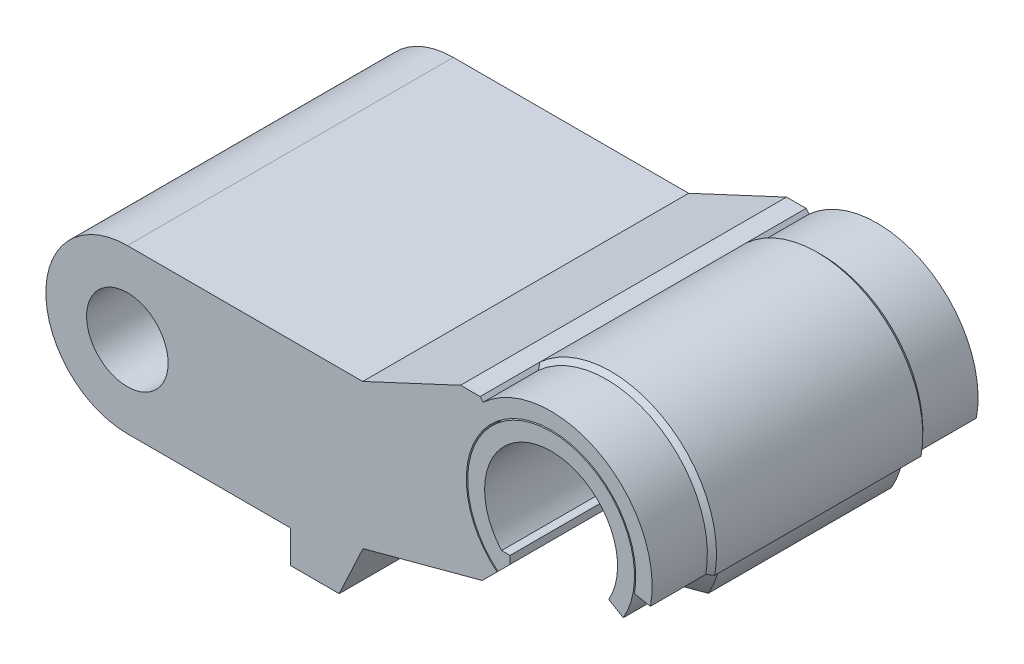
SolidWorks part; units mm, degrees
ref_plane "Front Plane" through (0, 0, 0) normal (0, 0, 1) x (1, 0, 0)
ref_plane "Top Plane" through (0, 0, 0) normal (0, 1, 0) x (1, 0, 0)
ref_plane "Right Plane" through (0, 0, 0) normal (1, 0, 0) x (0, 0, -1)
sketch "Sketch9" plane through (0, 0, 0) normal (0, 0, 1) x (1, 0, 0)
  line L0 (0, 0) -> (-40, 0) construction
  line L1 (-40, 0) -> (-40, -20) construction
  dimension "D1" = 20
  dimension "D2" = 40
sketch "Sketch1" plane through (0, 0, 0) normal (0, 0, 1) x (1, 0, 0)
  line L0 (7.5, -6.6144) -> (-7.5, -6.6144) construction
  line L1 (-7.5, -6.6144) -> (-6.3, -6.6144)
  line L2 (-6.3, -6.6144) -> (-6.3, 1.2617)
  line L3 (-6.3, 1.2617) -> (0, 4.899) construction
  line L4 (5, 4.899) -> (-5, 4.899) construction
  line L5 (0, -14.4444) -> (0, 14.4444) construction
  line L6 (-5.5, 5.199) -> (5.5, 5.199)
  line L7 (-6.3, 1.2617) -> (-3.7026, 2.7613)
  line L8 (0, 0) -> (-7.1429, 6.9985) construction
  line L9 (-5.5, 4.399) -> (-3.7026, 3.3613)
  line L10 (-5.5, 5.199) -> (-5.5, 4.399)
  line L11 (-3.7026, 3.3613) -> (-3.7026, 2.7613)
  line L12 (7.5, -6.6144) -> (6.3, -6.6144)
  line L13 (3.7026, 3.3613) -> (3.7026, 2.7613)
  line L14 (5.5, 5.199) -> (5.5, 4.399)
  line L15 (5.5, 4.399) -> (3.7026, 3.3613)
  line L16 (6.3, 1.2617) -> (3.7026, 2.7613)
  line L17 (6.3, -6.6144) -> (6.3, 1.2617)
  circle A0 centre (0, 0) radius 10 construction
  arc A1 (-7.5, -6.6144) -> (7.5, -6.6144) centre (0, 0) cw
  point P11 (0, 4.899)
  point P14 (0, 0)
sketch "Sketch2" plane through (0, 0, 0) normal (-1, 0, 0) x (0, 0, 1)
  line L0 (0, 10) -> (0, 15)
  line L3 (0, 15) -> (-3, 15)
  line L4 (-3, 15) -> (-9, 9)
  line L5 (-9, 9) -> (0, 9)
  line L6 (0, 9) -> (0, 10)
sketch "Sketch11" plane through (-40, -20, 0) normal (0, 0, -1) x (-1, 0, 0)
  line L0 (0, 0) -> (0, -150.5823)
  line L1 (0, 0) -> (15, 0)
  line L2 (15, 0) -> (43.25, -60.5823)
  line L3 (43.25, -60.5823) -> (53.25, -60.5823)
  line L4 (53.25, -60.5823) -> (53.25, -150.5823)
  line L5 (53.25, -150.5823) -> (72.25, -150.5823)
  line L6 (91.25, -150.5823) -> (91.25, -10.5823)
  line L7 (91.25, -10.5823) -> (114.25, -10.5823)
  line L8 (114.25, -10.5823) -> (114.25, -150.5823)
  line L9 (72.25, -150.5823) -> (91.25, -150.5823)
sketch "Sketch3" plane through (0, 0, 0) normal (0, 0, 1) x (1, 0, 0)
  line L0 (0, 15) -> (0, 15.2) construction
  line L1 (6.3, -8.0144) -> (9.8566, -11.571)
  line L2 (6.3, -6.8144) -> (6.3, -8.0144)
  line L16 (-6.3, -6.8144) -> (-6.3, -8.0144)
  line L17 (-6.3, -8.0144) -> (-9.8566, -11.571)
  line L18 (6.3, -6.8144) -> (7.5897, -6.8144)
  line L19 (-7.5897, -6.8144) -> (-6.3, -6.8144)
  line L20 (6.3, -6.8144) -> (7.5897, -6.8144)
  line L21 (-7.5897, -6.8144) -> (-6.3, -6.8144)
  arc A4 (-9.8566, -11.571) -> (9.8566, -11.571) centre (0, 0) cw
  arc A5 (7.5897, -6.8144) -> (-7.5897, -6.8144) centre (0, 0) ccw
  arc A6 (7.5897, -6.8144) -> (-7.5897, -6.8144) centre (0, 0) ccw
  point P4 (0, 15.1)
  point P5 (-10.1479, -11.3164)
  point P6 (-10.1104, -11.3499)
  point P10 (-9.8161, -11.5305)
  point P11 (0, 0)
  point P12 (0, 15.4202)
  dimension "D3" = 45
  dimension "D2" = 0.2
  dimension "D4" = 1.2
  dimension "D1" = 0.2
extrude "Boss-Extrude1" add sketch "Sketch3" along normal mid plane 50
sketch "Sketch4" plane through (0, 0, 0) normal (1, 0, 0) x (0, 0, -1)
  line L0 (0, 15) -> (0, 15.2) construction
  line L4 (-3.0828, 15.2) -> (-9.4828, 8.8)
  line L7 (9.4828, 8.8) -> (0, 8.8)
  line L8 (3.0828, 15.2) -> (9.4828, 8.8)
  line L9 (0, 15.2) -> (3.0828, 15.2)
  line L10 (9.4828, 8.8) -> (-9.4828, 8.8)
  line L11 (3.0828, 15.2) -> (9.4828, 8.8)
  line L12 (-3.0828, 15.2) -> (3.0828, 15.2)
  point P4 (0, 15.1878)
  dimension "D1" = 0.2
extrude "Cut-Extrude1" cut sketch "Sketch4" against normal mid plane 5.2
sketch "Sketch5" plane through (0, 0, 0) normal (1, 0, 0) x (0, 0, -1)
  line L0 (-25, 15.2) -> (-3.0828, 15.2)
  line L4 (3.0828, 15.2) -> (25, 15.2)
  line L5 (3.0828, 15.2) -> (25, 15.2) construction
  line L6 (25, 15.2) -> (25, 12.8)
  line L7 (25, 12.8) -> (16.4414, 12.8)
  line L8 (16.4414, 12.8) -> (14.0414, 15.2)
  line L9 (14.0414, 15.2) -> (25, 15.2)
  line L10 (25, 15.2) -> (3.0828, 15.2) construction
  line L11 (-27.2236, 0) -> (27.2236, 0) construction
  point P18 (0, 0)
  dimension "D1" = 45
  dimension "D2" = 2.4
revolve "Cut-Revolve1" cut sketch "Sketch5" angle 360 about L11
mirror "Mirror1" about plane through (0, 0, 0) normal (0, 0, 1) of "Cut-Revolve1"
sketch "Sketch7" plane through (0, 0, 0) normal (1, 0, 0) x (0, 0, -1)
  line L0 (16.4414, 12.8) -> (14.0414, 15.2)
  line L1 (16.4414, 12.8) -> (14.0414, 15.2) construction
  line L2 (25, 12.8) -> (16.4414, 12.8)
  line L3 (25, 12.8) -> (16.4414, 12.8) construction
  line L9 (-29.9525, 0) -> (29.9525, 0) construction
  line L10 (0, 0) -> (0, 27.8077) construction
  line L11 (-14.0414, 15.2) -> (-3.0828, 15.2)
  line L12 (3.0828, 15.2) -> (14.0414, 15.2)
  line L13 (3.0828, 15.2) -> (14.0414, 15.2) construction
  line L14 (25, 13) -> (16.5243, 13)
  line L15 (16.5243, 13) -> (14.1243, 15.4)
  line L16 (3.0828, 15.4) -> (14.1243, 15.4)
  line L17 (3.0828, 15.4) -> (-3.0828, 15.4)
  line L18 (-3.0828, 15.4) -> (-14.1243, 15.4)
  line L19 (-16.5243, 13) -> (-14.1243, 15.4)
  line L20 (-25, 13) -> (-16.5243, 13)
  line L22 (25, 13) -> (25, 15.5)
  line L23 (25, 15.5) -> (16.5243, 15.5)
  line L24 (16.5243, 15.5) -> (15.8243, 16.2)
  line L25 (15.8243, 16.2) -> (-15.8243, 16.2)
  line L26 (-3.0828, 15.2) -> (-14.0414, 15.2) construction
  line L27 (-16.4414, 12.8) -> (-14.0414, 15.2) construction
  line L28 (-16.5243, 15.5) -> (-15.8243, 16.2)
  line L29 (-25, 15.5) -> (-16.5243, 15.5)
  line L30 (-25, 13) -> (-25, 15.5)
  point P3 (16.8282, 16.2359)
  point P12 (0, 0)
  point P22 (0, 15.4)
  point P26 (0, 25)
  point P29 (15.3099, 16.2)
  point P32 (0, 16.2)
  dimension "D2" = 0.8
  dimension "D3" = 2.5
  dimension "D1" = 0.2
revolve "Revolve1" add sketch "Sketch7" angle 360 about L9
sketch "Sketch10" plane through (0, 0, 0) normal (0, 0, 1) x (1, 0, 0)
  line L0 (-6.3, -8.0144) -> (-9.8566, -11.571)
  line L1 (-6.3, -8.0144) -> (-9.8566, -11.571)
  line L2 (-9.8566, -11.571) -> (-28.2856, -30)
  line L5 (0, -14.4444) -> (0, 14.4444) construction
  line L6 (0, 0) -> (0, -30) construction
  line L9 (-6.3, -8.0144) -> (0, 0)
  line L10 (-28.2856, -30) -> (0, -30)
  line L11 (0, 0) -> (29.5047, -5.4288)
  line L12 (-9.8566, -11.571) -> (0, 0) construction
  arc A0 (29.5047, -5.4288) -> (0, -30) centre (0, 0) cw
  point P6 (0, -0.5784)
  dimension "D1" = 120
  dimension "D2" = 30
extrude "Cut-Extrude2" cut sketch "Sketch10" against normal through all both and the other way through all
sketch "Sketch12" plane through (0, 0, 0) normal (0, 0, 1) x (1, 0, 0)
  line L0 (-40, -20) -> (-40, -25)
  line L1 (-40, -20) -> (-40, -170.5823) construction
  line L2 (-40, -25) -> (-32.5, -25)
  line L3 (-32.5, -25) -> (-28.8537, -17.1804)
  line L4 (-28.8537, -17.1804) -> (-10.5658, -12.2802)
  line L5 (-9.9985, -11.7128) -> (-10.5658, -12.2802)
  line L6 (-9.9985, -11.7128) -> (-10.5658, -12.2802) construction
  line L7 (-40, -20) -> (-65, -20)
  line L8 (-28.8946, 5) -> (-65, 5)
  line L9 (-65, 5) -> (-65, -20) construction
  line L10 (-10.883, 12) -> (-13.883, 12)
  line L11 (-13.883, 12) -> (-28.8946, 5)
  arc A0 (15.9325, -2.9315) -> (-10.5658, -12.2802) centre (0, 0) ccw
  arc A1 (15.9325, -2.9315) -> (-10.5658, -12.2802) centre (0, 0) ccw construction
  arc A2 (-65, 5) -> (-65, -20) centre (-65, -7.5) ccw
  arc A3 (-10.883, 12) -> (-10.5658, -12.2802) centre (0, 0) ccw
  point P10 (0, 0)
  dimension "D1" = 5
  dimension "D2" = 7.5
  dimension "D3" = 115
  dimension "D4" = 130
  dimension "D5" = 10
  dimension "D6" = 25
  dimension "D7" = 3
  dimension "D8" = 25
  dimension "D9" = 7
extrude "Boss-Extrude2" add sketch "Sketch12" along normal mid plane 50
sketch "Sketch13" plane through (0, 0, -25) normal (0, 0, -1) x (-1, 0, 0)
  line L0 (10.883, 12) -> (10.4128, 11.4815)
  line L1 (10.0694, -11.7838) -> (10.5658, -12.2802)
  line L2 (-15.2441, -2.8049) -> (-12.7854, -2.3525)
  line L3 (8.2951, -10.0095) -> (10.0694, -11.7838)
  line L8 (40, -20) -> (65, -20)
  line L9 (65, 5) -> (28.8946, 5)
  line L10 (28.8946, 5) -> (13.883, 12)
  line L11 (13.883, 12) -> (10.883, 12)
  line L12 (10.5658, -12.2802) -> (28.8537, -17.1804)
  line L13 (28.8537, -17.1804) -> (32.5, -25)
  line L14 (32.5, -25) -> (40, -25)
  line L15 (40, -25) -> (40, -20)
  arc A0 (10.0694, -11.7838) -> (10.4128, 11.4815) centre (0, 0) ccw
  arc A2 (65, -20) -> (65, 5) centre (65, -7.5) ccw
  arc A3 (10.5658, -12.2802) -> (10.883, 12) centre (0, 0) ccw
  arc A5 (10.5658, -12.2802) -> (10.883, 12) centre (0, 0) ccw
  arc A6 (10.0694, -11.7838) -> (-15.2441, -2.8049) centre (0, 0) ccw
  arc A7 (8.2951, -10.0095) -> (-12.7854, -2.3525) centre (0, 0) ccw
  arc A8 (10.0694, -11.7838) -> (-15.2441, -2.8049) centre (0, 0) ccw construction
  dimension "D1" = 0
  dimension "D2" = 0
extrude "Boss-Extrude3" add sketch "Sketch13" against normal up to vertex
mirror "Mirror2" about plane through (0, 0, 0) normal (0, 0, 1) of "Boss-Extrude3"
sketch "Sketch15" plane through (0, 0, 0) normal (0, 0, 1) x (1, 0, 0)
  arc A0 (-65, 5) -> (-65, -20) centre (-65, -7.5) ccw
  arc A1 (-65, 5) -> (-65, -20) centre (-65, -7.5) ccw construction
  circle A2 centre (-65, -7.5) radius 6.25
  dimension "D1" = 12.5
extrude "Cut-Extrude3" cut sketch "Sketch15" against normal through all both and the other way through all
sketch "Sketch16" plane through (0, 0, 0) normal (0, 0, 1) x (1, 0, 0)
  line L0 (0, 0) -> (13.1636, -7.6)
  line L1 (0, -15.2) -> (0, 0)
  arc A0 (9.8566, -11.571) -> (-9.8566, -11.571) centre (0, 0) ccw construction
  arc A1 (13.1636, -7.6) -> (0, -15.2) centre (0, 0) cw
  dimension "D1" = 60
extrude "Cut-Extrude4" cut sketch "Sketch16" against normal through all both and the other way through all
